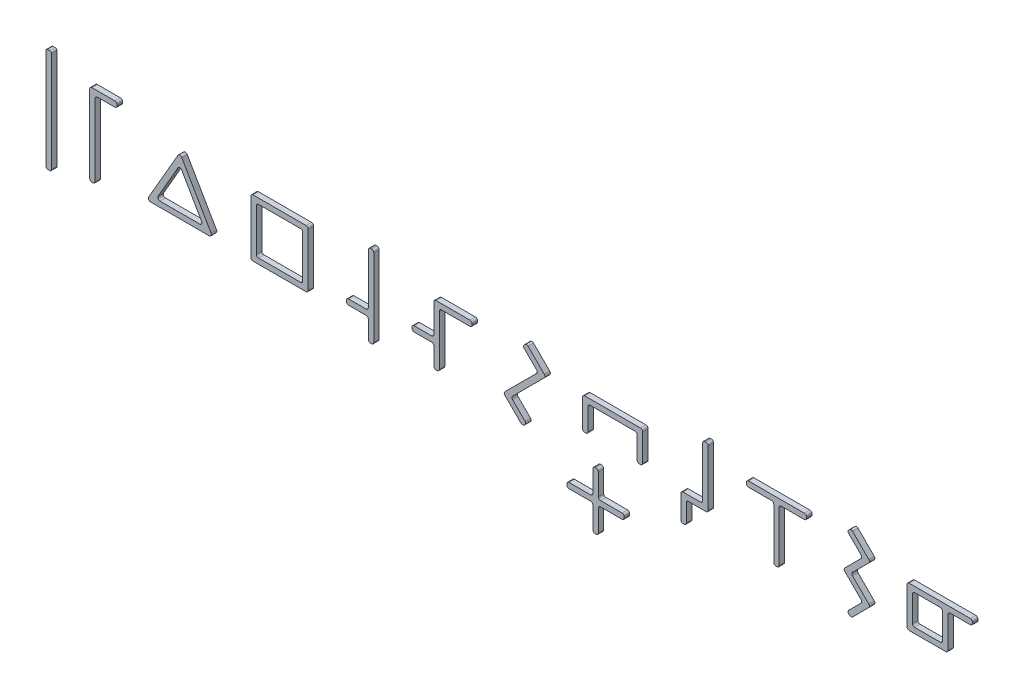
SolidWorks part; units mm, degrees
ref_plane "Front" through (0, 0, 0) normal (0, 0, 1) x (1, 0, 0)
ref_plane "Top" through (0, 0, 0) normal (0, 1, 0) x (1, 0, 0)
ref_plane "Right" through (0, 0, 0) normal (1, 0, 0) x (0, 0, -1)
sketch "Sketch1" plane through (0, 0, 0) normal (0, 0, 1) x (1, 0, 0)
  line L0 (0, 0) -> (422.4066, 0) construction
  line L1 (79, 75) -> (121, 75)
  line L2 (2, -95) -> (-2, -95)
  line L3 (5, -92) -> (5, 92)
  line L4 (2, 95) -> (-2, 95)
  line L5 (-5, -92) -> (-5, 92)
  line L6 (5, -95) -> (-5, 95) construction
  line L7 (5, 95) -> (-5, -95) construction
  line L8 (75, 75) -> (85, 75) construction
  line L9 (75, 71) -> (75, -71)
  line L10 (79, -75) -> (81, -75)
  line L11 (85, 75) -> (85, -75) construction
  line L12 (75, 75) -> (85, -75) construction
  line L13 (75, -75) -> (85, 75) construction
  line L14 (125, 71) -> (125, 69)
  line L15 (121, 65) -> (89, 65)
  line L16 (85, 61) -> (85, -71)
  line L17 (237.1249, 40.3284) -> (165, -31.7965)
  line L18 (165, -37.4533) -> (166.4142, -38.8675)
  line L19 (172.0711, -38.8675) -> (237.1249, 26.1863)
  line L20 (242.7817, 26.1863) -> (307.8356, -38.8675)
  line L21 (313.4924, -38.8675) -> (314.9066, -37.4533)
  line L22 (314.9066, -31.7965) -> (242.7817, 40.3284)
  line L23 (239.9533, 37.5) -> (239.9533, 0) construction
  line L24 (422.4066, 0) -> (878.0402, 0) construction
  line L25 (470.9066, -52.5) -> (373.9066, -52.5)
  line L26 (474.9066, -48.5) -> (474.9066, 48.5)
  line L27 (470.9066, 52.5) -> (373.9066, 52.5)
  line L28 (369.9066, -48.5) -> (369.9066, 48.5)
  line L29 (474.9066, -52.5) -> (369.9066, 52.5) construction
  line L30 (474.9066, 52.5) -> (369.9066, -52.5) construction
  line L31 (460.9066, -42.5) -> (383.9066, -42.5)
  line L32 (464.9066, -38.5) -> (464.9066, 38.5)
  line L33 (460.9066, 42.5) -> (383.9066, 42.5)
  line L34 (379.9066, -38.5) -> (379.9066, 38.5)
  line L35 (464.9066, -42.5) -> (379.9066, 42.5) construction
  line L36 (464.9066, 42.5) -> (379.9066, -42.5) construction
  line L37 (584.9066, 71) -> (584.9066, -21)
  line L38 (580.9066, -25) -> (548.9066, -25)
  line L39 (544.9066, -29) -> (544.9066, -31)
  line L40 (548.9066, -35) -> (580.9066, -35)
  line L41 (584.9066, -39) -> (584.9066, -71)
  line L42 (588.9066, -75) -> (590.9066, -75)
  line L43 (594.9066, -71) -> (594.9066, 71)
  line L44 (588.9066, 75) -> (590.9066, 75)
  line L45 (664.9066, -11.5) -> (664.9066, -13.5)
  line L46 (668.9066, -17.5) -> (700.9066, -17.5)
  line L47 (704.9066, -21.5) -> (704.9066, -53.5)
  line L48 (708.9066, -57.5) -> (710.9066, -57.5)
  line L49 (714.9066, -53.5) -> (714.9066, 38.5)
  line L50 (718.9066, 42.5) -> (770.9066, 42.5)
  line L51 (774.9066, 46.5) -> (774.9066, 48.5)
  line L52 (770.9066, 52.5) -> (708.9066, 52.5)
  line L53 (704.9066, 48.5) -> (704.9066, -3.5)
  line L54 (700.9066, -7.5) -> (668.9066, -7.5)
  line L55 (881.5757, 67.1751) -> (846.2203, 31.8198) construction
  line L56 (846.2203, 31.8198) -> (909.86, -31.8198) construction
  line L57 (909.86, -31.8198) -> (881.5757, -60.1041) construction
  line L58 (881.5757, -60.1041) -> (888.6468, -67.1751) construction
  line L59 (888.6468, -67.1751) -> (924.0021, -31.8198) construction
  line L60 (924.0021, -31.8198) -> (860.3625, 31.8198) construction
  line L61 (860.3625, 31.8198) -> (888.6468, 60.1041) construction
  line L62 (888.6468, 60.1041) -> (881.5757, 67.1751) construction
  line L63 (892.1823, 0) -> (878.0402, 0) construction
  line L64 (878.0402, 0) -> (878.0402, 24.2685) construction
  line L65 (909.86, 31.8198) -> (874.5046, -60.1041) construction
  line L66 (870.262, 62.9325) -> (871.6762, 64.3467)
  line L67 (892.8894, 34.6482) -> (870.262, 57.2756)
  line L68 (834.9066, -28.9914) -> (892.8894, 28.9914)
  line L69 (864.6051, -64.3467) -> (834.9066, -34.6482)
  line L70 (871.6762, -62.9325) -> (870.262, -64.3467)
  line L71 (849.0488, -34.6482) -> (871.6762, -57.2756)
  line L72 (907.0315, 28.9914) -> (849.0488, -28.9914)
  line L73 (877.333, 64.3467) -> (907.0315, 34.6482)
  line L74 (892.1823, 0) -> (1489.5584, 0) construction
  line L75 (977.0315, 33.5) -> (977.0315, -16.5)
  line L76 (981.0315, -20.5) -> (983.0315, -20.5)
  line L77 (987.0315, -16.5) -> (987.0315, 23.5)
  line L78 (991.0315, 27.5) -> (1073.0315, 27.5)
  line L79 (1077.0315, 23.5) -> (1077.0315, -16.5)
  line L80 (1081.0315, -20.5) -> (1083.0315, -20.5)
  line L81 (1087.0315, -16.5) -> (1087.0315, 33.5)
  line L82 (1083.0315, 37.5) -> (981.0315, 37.5)
  line L83 (1157.0315, -29) -> (1157.0315, -71)
  line L84 (1161.0315, -75) -> (1163.0315, -75)
  line L85 (1167.0315, -71) -> (1167.0315, -39)
  line L86 (1171.0315, -35) -> (1203.0315, -35)
  line L87 (1207.0315, -31) -> (1207.0315, 71)
  line L88 (1203.0315, 75) -> (1201.0315, 75)
  line L89 (1197.0315, 71) -> (1197.0315, -21)
  line L90 (1193.0315, -25) -> (1161.0315, -25)
  line L91 (1277.0315, 48.5) -> (1277.0315, 46.5)
  line L92 (1281.0315, 42.5) -> (1323.0315, 42.5)
  line L93 (1327.0315, 38.5) -> (1327.0315, -53.5)
  line L94 (1331.0315, -57.5) -> (1333.0315, -57.5)
  line L95 (1337.0315, -53.5) -> (1337.0315, 38.5)
  line L96 (1341.0315, 42.5) -> (1383.0315, 42.5)
  line L97 (1387.0315, 46.5) -> (1387.0315, 48.5)
  line L98 (1383.0315, 52.5) -> (1281.0315, 52.5)
  line L99 (1332.0315, -57.5) -> (1332.0315, 52.5) construction
  line L100 (1486.73, 67.8823) -> (1457.0315, 38.1838) construction
  line L101 (1457.0315, 32.5269) -> (1486.73, 2.8284) construction
  line L102 (1486.73, -2.8284) -> (1457.0315, -32.5269) construction
  line L103 (1457.0315, -38.1838) -> (1486.73, -67.8823) construction
  line L104 (1492.3869, -67.8823) -> (1493.8011, -66.468) construction
  line L105 (1493.8011, -60.8112) -> (1471.1737, -38.1838) construction
  line L106 (1471.1737, -32.5269) -> (1500.8721, -2.8284) construction
  line L107 (1500.8721, 2.8284) -> (1471.1737, 32.5269) construction
  line L108 (1471.1737, 38.1838) -> (1493.8011, 60.8112) construction
  line L109 (1493.8011, 66.468) -> (1492.3869, 67.8823) construction
  line L110 (1489.5584, 0) -> (1580.8721, 0) construction
  line L111 (1570.8721, 33.5) -> (1570.8721, -33.5)
  line L112 (1574.8721, -37.5) -> (1641.8721, -37.5)
  line L113 (1645.8721, -33.5) -> (1645.8721, 23.5)
  line L114 (1649.8721, 27.5) -> (1686.8721, 27.5)
  line L115 (1690.8721, 31.5) -> (1690.8721, 33.5)
  line L116 (1686.8721, 37.5) -> (1574.8721, 37.5)
  line L117 (1580.8721, 23.5) -> (1580.8721, -23.5)
  line L118 (1584.8721, -27.5) -> (1631.8721, -27.5)
  line L119 (1635.8721, -23.5) -> (1635.8721, 23.5)
  line L120 (1631.8721, 27.5) -> (1584.8721, 27.5)
  line L121 (221.0212, 42.5) -> (221.0212, -42.5) construction
  line L122 (221.0212, 0) -> (242.7088, 0) construction
  line L123 (221.0212, -42.5) -> (258.1213, -42.5) construction
  line L124 (221.0212, 42.5) -> (250.1418, 42.5) construction
  line L125 (1479.0071, 75.8721) -> (1479.0071, -71) construction
  line L126 (1464.2131, 66.468) -> (1465.6273, 67.8823)
  line L127 (1486.8405, 38.1838) -> (1464.2131, 60.8112)
  line L128 (1457.142, 2.8284) -> (1486.8405, 32.5269)
  line L129 (1486.8405, -32.5269) -> (1457.142, -2.8284)
  line L130 (1464.2131, -60.8112) -> (1486.8405, -38.1838)
  line L131 (1465.6273, -67.8823) -> (1464.2131, -66.468)
  line L132 (1500.9826, -38.1838) -> (1471.2842, -67.8823)
  line L133 (1471.2842, -2.8284) -> (1500.9826, -32.5269)
  line L134 (1500.9826, 32.5269) -> (1471.2842, 2.8284)
  line L135 (1471.2842, 67.8823) -> (1500.9826, 38.1838)
  arc A0 (-2, -95) -> (-5, -92) centre (-2, -92) cw
  arc A1 (2, -95) -> (5, -92) centre (2, -92) ccw
  arc A2 (5, 92) -> (2, 95) centre (2, 92) ccw
  arc A3 (-2, 95) -> (-5, 92) centre (-2, 92) ccw
  arc A4 (75, -71) -> (79, -75) centre (79, -71) ccw
  arc A5 (81, -75) -> (85, -71) centre (81, -71) ccw
  arc A6 (89, 65) -> (85, 61) centre (89, 61) ccw
  arc A7 (125, 69) -> (121, 65) centre (121, 69) cw
  arc A8 (121, 75) -> (125, 71) centre (121, 71) cw
  arc A9 (79, 75) -> (75, 71) centre (79, 71) ccw
  arc A10 (314.9066, -37.4533) -> (314.9066, -31.7965) centre (312.0782, -34.6249) ccw
  arc A11 (307.8356, -38.8675) -> (313.4924, -38.8675) centre (310.664, -36.0391) ccw
  arc A12 (237.1249, 26.1863) -> (242.7817, 26.1863) centre (239.9533, 23.3579) cw
  arc A13 (237.1249, 40.3284) -> (242.7817, 40.3284) centre (239.9533, 37.5) cw
  arc A14 (166.4142, -38.8675) -> (172.0711, -38.8675) centre (169.2426, -36.0391) ccw
  arc A15 (165, -31.7965) -> (165, -37.4533) centre (167.8284, -34.6249) ccw
  arc A16 (373.9066, -52.5) -> (369.9066, -48.5) centre (373.9066, -48.5) cw
  arc A17 (383.9066, -42.5) -> (379.9066, -38.5) centre (383.9066, -38.5) cw
  arc A18 (460.9066, -42.5) -> (464.9066, -38.5) centre (460.9066, -38.5) ccw
  arc A19 (470.9066, -52.5) -> (474.9066, -48.5) centre (470.9066, -48.5) ccw
  arc A20 (464.9066, 38.5) -> (460.9066, 42.5) centre (460.9066, 38.5) ccw
  arc A21 (474.9066, 48.5) -> (470.9066, 52.5) centre (470.9066, 48.5) ccw
  arc A22 (373.9066, 52.5) -> (369.9066, 48.5) centre (373.9066, 48.5) ccw
  arc A23 (383.9066, 42.5) -> (379.9066, 38.5) centre (383.9066, 38.5) ccw
  arc A24 (708.9066, 52.5) -> (704.9066, 48.5) centre (708.9066, 48.5) ccw
  arc A25 (774.9066, 48.5) -> (770.9066, 52.5) centre (770.9066, 48.5) ccw
  arc A26 (770.9066, 42.5) -> (774.9066, 46.5) centre (770.9066, 46.5) ccw
  arc A27 (714.9066, 38.5) -> (718.9066, 42.5) centre (718.9066, 38.5) cw
  arc A28 (710.9066, -57.5) -> (714.9066, -53.5) centre (710.9066, -53.5) ccw
  arc A29 (704.9066, -53.5) -> (708.9066, -57.5) centre (708.9066, -53.5) ccw
  arc A30 (704.9066, -3.5) -> (700.9066, -7.5) centre (700.9066, -3.5) cw
  arc A31 (700.9066, -17.5) -> (704.9066, -21.5) centre (700.9066, -21.5) cw
  arc A32 (664.9066, -11.5) -> (668.9066, -7.5) centre (668.9066, -11.5) cw
  arc A33 (664.9066, -13.5) -> (668.9066, -17.5) centre (668.9066, -13.5) ccw
  arc A34 (544.9066, -31) -> (548.9066, -35) centre (548.9066, -31) ccw
  arc A35 (548.9066, -25) -> (544.9066, -29) centre (548.9066, -29) ccw
  arc A36 (584.9066, -21) -> (580.9066, -25) centre (580.9066, -21) cw
  arc A37 (580.9066, -35) -> (584.9066, -39) centre (580.9066, -39) cw
  arc A38 (584.9066, -71) -> (588.9066, -75) centre (588.9066, -71) ccw
  arc A39 (590.9066, -75) -> (594.9066, -71) centre (590.9066, -71) ccw
  arc A40 (594.9066, 71) -> (590.9066, 75) centre (590.9066, 71) ccw
  arc A41 (584.9066, 71) -> (588.9066, 75) centre (588.9066, 71) cw
  arc A42 (1083.0315, -20.5) -> (1087.0315, -16.5) centre (1083.0315, -16.5) ccw
  arc A43 (1077.0315, -16.5) -> (1081.0315, -20.5) centre (1081.0315, -16.5) ccw
  arc A44 (983.0315, -20.5) -> (987.0315, -16.5) centre (983.0315, -16.5) ccw
  arc A45 (977.0315, -16.5) -> (981.0315, -20.5) centre (981.0315, -16.5) ccw
  arc A46 (987.0315, 23.5) -> (991.0315, 27.5) centre (991.0315, 23.5) cw
  arc A47 (1073.0315, 27.5) -> (1077.0315, 23.5) centre (1073.0315, 23.5) cw
  arc A48 (1087.0315, 33.5) -> (1083.0315, 37.5) centre (1083.0315, 33.5) ccw
  arc A49 (977.0315, 33.5) -> (981.0315, 37.5) centre (981.0315, 33.5) cw
  arc A50 (1157.0315, -71) -> (1161.0315, -75) centre (1161.0315, -71) ccw
  arc A51 (1163.0315, -75) -> (1167.0315, -71) centre (1163.0315, -71) ccw
  arc A52 (1167.0315, -39) -> (1171.0315, -35) centre (1171.0315, -39) cw
  arc A53 (1157.0315, -29) -> (1161.0315, -25) centre (1161.0315, -29) cw
  arc A54 (1197.0315, -21) -> (1193.0315, -25) centre (1193.0315, -21) cw
  arc A55 (1203.0315, -35) -> (1207.0315, -31) centre (1203.0315, -31) ccw
  arc A56 (1207.0315, 71) -> (1203.0315, 75) centre (1203.0315, 71) ccw
  arc A57 (1201.0315, 75) -> (1197.0315, 71) centre (1201.0315, 71) ccw
  arc A58 (1277.0315, 48.5) -> (1281.0315, 52.5) centre (1281.0315, 48.5) cw
  arc A59 (1277.0315, 46.5) -> (1281.0315, 42.5) centre (1281.0315, 46.5) ccw
  arc A60 (1323.0315, 42.5) -> (1327.0315, 38.5) centre (1323.0315, 38.5) cw
  arc A61 (1327.0315, -53.5) -> (1331.0315, -57.5) centre (1331.0315, -53.5) ccw
  arc A62 (1333.0315, -57.5) -> (1337.0315, -53.5) centre (1333.0315, -53.5) ccw
  arc A63 (1337.0315, 38.5) -> (1341.0315, 42.5) centre (1341.0315, 38.5) cw
  arc A64 (1383.0315, 42.5) -> (1387.0315, 46.5) centre (1383.0315, 46.5) ccw
  arc A65 (1387.0315, 48.5) -> (1383.0315, 52.5) centre (1383.0315, 48.5) ccw
  arc A66 (1457.0315, -32.5269) -> (1457.0315, -38.1838) centre (1459.86, -35.3553) ccw construction
  arc A67 (1486.73, -67.8823) -> (1492.3869, -67.8823) centre (1489.5584, -65.0538) ccw construction
  arc A68 (1493.8011, -66.468) -> (1493.8011, -60.8112) centre (1490.9727, -63.6396) ccw construction
  arc A69 (1471.1737, -38.1838) -> (1471.1737, -32.5269) centre (1474.0021, -35.3553) cw construction
  arc A70 (1457.0315, 38.1838) -> (1457.0315, 32.5269) centre (1459.86, 35.3553) ccw construction
  arc A71 (1486.73, -2.8284) -> (1486.73, 2.8284) centre (1483.9016, 0) ccw construction
  arc A72 (1500.8721, -2.8284) -> (1500.8721, 2.8284) centre (1498.0437, 0) ccw construction
  arc A73 (1471.1737, 32.5269) -> (1471.1737, 38.1838) centre (1474.0021, 35.3553) cw construction
  arc A74 (1493.8011, 60.8112) -> (1493.8011, 66.468) centre (1490.9727, 63.6396) ccw construction
  arc A75 (1486.73, 67.8823) -> (1492.3869, 67.8823) centre (1489.5584, 65.0538) cw construction
  arc A76 (1690.8721, 33.5) -> (1686.8721, 37.5) centre (1686.8721, 33.5) ccw
  arc A77 (1686.8721, 27.5) -> (1690.8721, 31.5) centre (1686.8721, 31.5) ccw
  arc A78 (1645.8721, 23.5) -> (1649.8721, 27.5) centre (1649.8721, 23.5) cw
  arc A79 (1641.8721, -37.5) -> (1645.8721, -33.5) centre (1641.8721, -33.5) ccw
  arc A80 (1570.8721, -33.5) -> (1574.8721, -37.5) centre (1574.8721, -33.5) ccw
  arc A81 (1580.8721, -23.5) -> (1584.8721, -27.5) centre (1584.8721, -23.5) ccw
  arc A82 (1631.8721, -27.5) -> (1635.8721, -23.5) centre (1631.8721, -23.5) ccw
  arc A83 (1635.8721, 23.5) -> (1631.8721, 27.5) centre (1631.8721, 23.5) ccw
  arc A84 (1580.8721, 23.5) -> (1584.8721, 27.5) centre (1584.8721, 23.5) cw
  arc A85 (1570.8721, 33.5) -> (1574.8721, 37.5) centre (1574.8721, 33.5) cw
  arc A86 (864.6051, -64.3467) -> (870.262, -64.3467) centre (867.4335, -61.5183) ccw
  arc A87 (871.6762, -57.2756) -> (871.6762, -62.9325) centre (868.8478, -60.1041) cw
  arc A88 (849.0488, -34.6482) -> (849.0488, -28.9914) centre (851.8772, -31.8198) cw
  arc A89 (834.9066, -28.9914) -> (834.9066, -34.6482) centre (837.7351, -31.8198) ccw
  arc A90 (892.8894, 34.6482) -> (892.8894, 28.9914) centre (890.061, 31.8198) cw
  arc A91 (907.0315, 34.6482) -> (907.0315, 28.9914) centre (904.2031, 31.8198) cw
  arc A92 (870.262, 62.9325) -> (870.262, 57.2756) centre (873.0904, 60.1041) ccw
  arc A93 (871.6762, 64.3467) -> (877.333, 64.3467) centre (874.5046, 61.5183) cw
  arc A94 (1471.2842, 67.8823) -> (1465.6273, 67.8823) centre (1468.4557, 65.0538) ccw
  arc A95 (1464.2131, 60.8112) -> (1464.2131, 66.468) centre (1467.0415, 63.6396) cw
  arc A96 (1486.8405, 32.5269) -> (1486.8405, 38.1838) centre (1484.0121, 35.3553) ccw
  arc A97 (1457.142, -2.8284) -> (1457.142, 2.8284) centre (1459.9704, 0) cw
  arc A98 (1471.2842, -2.8284) -> (1471.2842, 2.8284) centre (1474.1126, 0) cw
  arc A99 (1500.9826, 38.1838) -> (1500.9826, 32.5269) centre (1498.1542, 35.3553) cw
  arc A100 (1486.8405, -38.1838) -> (1486.8405, -32.5269) centre (1484.0121, -35.3553) ccw
  arc A101 (1464.2131, -66.468) -> (1464.2131, -60.8112) centre (1467.0415, -63.6396) cw
  arc A102 (1471.2842, -67.8823) -> (1465.6273, -67.8823) centre (1468.4557, -65.0538) cw
  arc A103 (1500.9826, -32.5269) -> (1500.9826, -38.1838) centre (1498.1542, -35.3553) cw
  point P7 (80, 0)
  point P35 (85, 65)
  point P43 (80, -75)
  point P71 (422.4066, -52.5)
  point P146 (584.9066, -75)
  point P149 (594.9066, -75)
  point P239 (1486.0229, -17.6777)
  point P241 (1493.094, 67.1751)
  point P311 (867.4335, -67.1751)
  point P317 (846.2203, -31.8198)
  point P320 (832.0782, -31.8198)
  point P323 (895.7178, 31.8198)
  point P329 (867.4335, 60.1041)
  point P332 (874.5046, 67.1751)
  point P334 (1580.8721, 0)
  dimension "D4" = 3
  dimension "D5" = 4
  dimension "D15" = 4
  dimension "D20" = 4
  dimension "D34" = 4
  dimension "D47" = 4
  dimension "D54" = 4
  dimension "D68" = 4
  dimension "D69" = 4
  dimension "D77" = 4
  dimension "D78" = 4
  dimension "D1" = 190
  dimension "D2" = 10
  dimension "D3" = 50
  dimension "D6" = 150
  dimension "D7" = 10
  dimension "D8" = 10
  dimension "D9" = 70
  dimension "D10" = 10
  dimension "D11" = 10
  dimension "D12" = 110
  dimension "D13" = 110
  dimension "D14" = 45
  dimension "D16" = 10
  dimension "D17" = 105
  dimension "D18" = 10
  dimension "D19" = 105
  dimension "D21" = 10
  dimension "D22" = 10
  dimension "D23" = 150
  dimension "D24" = 50
  dimension "D25" = 10
  dimension "D26" = 40
  dimension "D27" = 10
  dimension "D28" = 10
  dimension "D29" = 10
  dimension "D30" = 10
  dimension "D31" = 110
  dimension "D32" = 50
  dimension "D33" = 40
  dimension "D35" = 10
  dimension "D36" = 10
  dimension "D37" = 10
  dimension "D38" = 50
  dimension "D39" = 50
  dimension "D40" = 100
  dimension "D41" = 45
  dimension "D42" = 10
  dimension "D43" = 10
  dimension "D44" = 10
  dimension "D45" = 110
  dimension "D46" = 58
  dimension "D48" = 10
  dimension "D49" = 10
  dimension "D50" = 10
  dimension "D51" = 50
  dimension "D52" = 110
  dimension "D53" = 50
  dimension "D55" = 10
  dimension "D56" = 10
  dimension "D57" = 110
  dimension "D58" = 110
  dimension "D59" = 10
  dimension "D60" = 10
  dimension "D61" = 10
  dimension "D62" = 10
  dimension "D63" = 50
  dimension "D64" = 50
  dimension "D65" = 50
  dimension "D66" = 50
  dimension "D67" = 45
  dimension "D70" = 10
  dimension "D71" = 10
  dimension "D72" = 10
  dimension "D73" = 10
  dimension "D74" = 75
  dimension "D75" = 75
  dimension "D76" = 120
  dimension "D79" = 70
  dimension "D80" = 70
  dimension "D81" = 70
  dimension "D82" = 70
  dimension "D83" = 70
  dimension "D84" = 60
  dimension "D85" = 70
  dimension "D86" = 70
  dimension "D87" = 70
  dimension "D88" = 55
  dimension "D89" = 40
  dimension "D90" = 85
extrude "Boss-Extrude1" add sketch "Sketch1" along normal blind 10
sketch "Sketch4" plane through (0, 0, 0) normal (0, 0, 1) x (1, 0, 0)
  line L1 (163.6688, 104.0609) -> (357.3487, 104.0609)
  line L2 (163.6688, 104.0609) -> (163.6688, -191.1045)
  line L3 (163.6688, -191.1045) -> (357.3487, -191.1045)
  line L4 (357.3487, 104.0609) -> (357.3487, -191.1045)
extrude "Cut-Extrude4" cut sketch "Sketch4" along normal through all
sketch "Sketch5" plane through (0, 0, 0) normal (0, 0, 1) x (1, 0, 0)
  line L0 (236.4892, 46.5) -> (182.7956, -46.5)
  line L1 (186.2597, -52.5) -> (293.6469, -52.5)
  line L2 (297.111, -46.5) -> (243.4174, 46.5)
  line L3 (239.9533, 52.5) -> (239.9533, -52.5) construction
  line L4 (440.4556, 52.5) -> (239.9533, 52.5) construction
  line L5 (470.9066, 52.5) -> (373.9066, 52.5) construction
  line L6 (203.5803, -42.5) -> (276.3264, -42.5)
  line L7 (279.7905, -36.5) -> (243.4174, 26.5)
  line L8 (236.4892, 26.5) -> (200.1162, -36.5)
  line L9 (239.9533, 52.5) -> (179.3315, -52.5) construction
  line L10 (179.3315, -52.5) -> (300.5751, -52.5) construction
  line L11 (300.5751, -52.5) -> (239.9533, 52.5) construction
  line L12 (196.652, -42.5) -> (283.2546, -42.5) construction
  line L13 (239.9533, 32.5) -> (196.652, -42.5) construction
  line L14 (283.2546, -42.5) -> (239.9533, 32.5) construction
  arc A0 (182.7956, -46.5) -> (186.2597, -52.5) centre (186.2597, -48.5) ccw
  arc A1 (293.6469, -52.5) -> (297.111, -46.5) centre (293.6469, -48.5) ccw
  arc A2 (236.4892, 46.5) -> (243.4174, 46.5) centre (239.9533, 44.5) cw
  arc A3 (203.5803, -42.5) -> (200.1162, -36.5) centre (203.5803, -38.5) cw
  arc A4 (276.3264, -42.5) -> (279.7905, -36.5) centre (276.3264, -38.5) ccw
  arc A5 (243.4174, 26.5) -> (236.4892, 26.5) centre (239.9533, 24.5) ccw
  point P2 (239.9533, 0)
  dimension "D2" = 4
  dimension "D3" = 4
  dimension "D1" = 10
extrude "Boss-Extrude3" add sketch "Sketch5" along normal up to surface (10 mm away) separate body up to face at (422.4066, 0, 10)
sketch "Sketch6" plane through (0, 0, 0) normal (0, 0, 1) x (1, 0, 0)
  line L1 (314.7545, 112.8077) -> (506.4784, 112.8077)
  line L2 (314.7545, 112.8077) -> (314.7545, -150.8126)
  line L3 (314.7545, -150.8126) -> (506.4784, -150.8126)
  line L4 (506.4784, 112.8077) -> (506.4784, -150.8126)
extrude "Cut-Extrude6" [suppressed] cut sketch "Sketch6" along normal through all
sketch "Sketch7" plane through (0, 0, 0) normal (0, 0, 1) x (1, 0, 0)
  line L2 (467.4066, -45) -> (377.4066, -45) construction
  line L3 (467.4066, -45) -> (467.4066, 45) construction
  line L4 (467.4066, 45) -> (377.4066, 45) construction
  line L7 (377.4066, -45) -> (377.4066, 45) construction
  line L8 (467.4066, -45) -> (377.4066, 45) construction
  line L9 (467.4066, 45) -> (377.4066, -45) construction
  line L10 (377.4066, 45) -> (407.4066, 45)
  line L12 (377.4066, 45) -> (377.4066, 35)
  line L13 (377.4066, 35) -> (407.4066, 35)
  line L14 (407.4066, 45) -> (407.4066, 35)
  line L15 (467.4066, 45) -> (437.4066, 45)
  line L16 (467.4066, 45) -> (467.4066, 35)
  line L17 (467.4066, 35) -> (437.4066, 35)
  line L18 (437.4066, 45) -> (437.4066, 35)
  line L19 (377.4066, -45) -> (407.4066, -45)
  line L20 (377.4066, -45) -> (377.4066, -35)
  line L21 (377.4066, -35) -> (407.4066, -35)
  line L22 (407.4066, -45) -> (407.4066, -35)
  line L23 (467.4066, -45) -> (437.4066, -45)
  line L24 (467.4066, -45) -> (467.4066, -35)
  line L25 (467.4066, -35) -> (437.4066, -35)
  line L26 (437.4066, -45) -> (437.4066, -35)
  point P0 (422.4066, 0)
  dimension "D1" = 90
  dimension "D2" = 10
  dimension "D3" = 30
extrude "Boss-Extrude4" [suppressed] add sketch "Sketch7" along normal up to surface (10 mm away) separate body
sketch "Sketch8" plane through (0, 0, 0) normal (0, 0, 1) x (1, 0, 0)
  line L1 (1053.3484, -66.5574) -> (948.3484, -66.5574) construction
  line L2 (1053.3484, -66.5574) -> (1053.3484, -171.5574) construction
  line L3 (1053.3484, -171.5574) -> (948.3484, -171.5574) construction
  line L4 (948.3484, -66.5574) -> (948.3484, -171.5574) construction
  line L5 (1053.3484, -66.5574) -> (948.3484, -171.5574) construction
  line L6 (1053.3484, -171.5574) -> (948.3484, -66.5574) construction
  line L8 (995.8484, -70.5574) -> (995.8484, -110.0574)
  line L9 (991.8484, -114.0574) -> (952.3484, -114.0574)
  line L10 (948.3484, -118.0574) -> (948.3484, -120.0574)
  line L11 (952.3484, -124.0574) -> (991.8484, -124.0574)
  line L12 (995.8484, -128.0574) -> (995.8484, -167.5574)
  line L13 (999.8484, -171.5574) -> (1001.8484, -171.5574)
  line L14 (1005.8484, -167.5574) -> (1005.8484, -128.0574)
  line L15 (1009.8484, -124.0574) -> (1049.3484, -124.0574)
  line L16 (1053.3484, -120.0574) -> (1053.3484, -118.0574)
  line L17 (1049.3484, -114.0574) -> (1009.8484, -114.0574)
  line L18 (1005.8484, -110.0574) -> (1005.8484, -70.5574)
  line L19 (1001.8484, -66.5574) -> (999.8484, -66.5574)
  line L20 (948.3484, -119.0574) -> (1053.3484, -119.0574) construction
  line L21 (1000.8484, -66.5574) -> (1000.8484, -171.5574) construction
  arc A0 (948.3484, -120.0574) -> (952.3484, -124.0574) centre (952.3484, -120.0574) ccw
  arc A1 (952.3484, -114.0574) -> (948.3484, -118.0574) centre (952.3484, -118.0574) ccw
  arc A2 (995.8484, -110.0574) -> (991.8484, -114.0574) centre (991.8484, -110.0574) cw
  arc A3 (991.8484, -124.0574) -> (995.8484, -128.0574) centre (991.8484, -128.0574) cw
  arc A4 (1005.8484, -128.0574) -> (1009.8484, -124.0574) centre (1009.8484, -128.0574) cw
  arc A5 (995.8484, -167.5574) -> (999.8484, -171.5574) centre (999.8484, -167.5574) ccw
  arc A6 (1001.8484, -171.5574) -> (1005.8484, -167.5574) centre (1001.8484, -167.5574) ccw
  arc A7 (1049.3484, -124.0574) -> (1053.3484, -120.0574) centre (1049.3484, -120.0574) ccw
  arc A8 (1053.3484, -118.0574) -> (1049.3484, -114.0574) centre (1049.3484, -118.0574) ccw
  arc A9 (1009.8484, -114.0574) -> (1005.8484, -110.0574) centre (1009.8484, -110.0574) cw
  arc A10 (1005.8484, -70.5574) -> (1001.8484, -66.5574) centre (1001.8484, -70.5574) ccw
  arc A11 (995.8484, -70.5574) -> (999.8484, -66.5574) centre (999.8484, -70.5574) cw
  point P0 (1000.8484, -119.0574)
  dimension "D3" = 4
  dimension "D1" = 10
  dimension "D2" = 10
extrude "Boss-Extrude5" add sketch "Sketch8" along normal up to surface (10 mm away) separate body up to face at (0, 0, 10)
